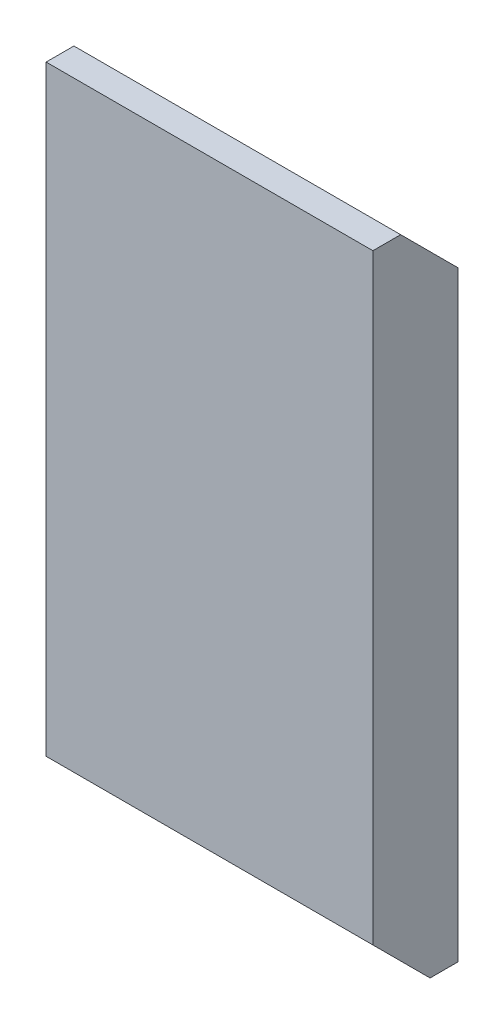
SolidWorks part; units mm, degrees
ref_plane "Front Plane" through (0, 0, 0) normal (0, 0, 1) x (1, 0, 0)
ref_plane "Top Plane" through (0, 0, 0) normal (0, 1, 0) x (1, 0, 0)
ref_plane "Right Plane" through (0, 0, 0) normal (1, 0, 0) x (0, 0, -1)
sketch "Sketch1" plane through (0, 0, 0) normal (0, 0, 1) x (1, 0, 0)
  line L2 (-12.7, -73.2155) -> (12.7, -73.2155)
  line L3 (-12.7, -73.2155) -> (-12.7, -22.0345)
  line L4 (12.7, -22.0345) -> (-12.7, -22.0345)
  line L5 (12.7, -73.2155) -> (12.7, -22.0345)
  point P2 (0, -22.0345)
  point P3 (0, -22.0345)
  point P4 (0, -50.8)
extrude "Boss-Extrude1" add sketch "Sketch1" along normal blind 6.604
sketch "Sketch2" plane through (0, 0, 0) normal (0, 0, -1) x (-1, 0, 0)
  text T0 "Groucho\r\n Fractal"
chamfer "Chamfer1" distance 4.445 angle 45 2 edges at (0, -73.2155, 6.604) (0, -22.0345, 0)
